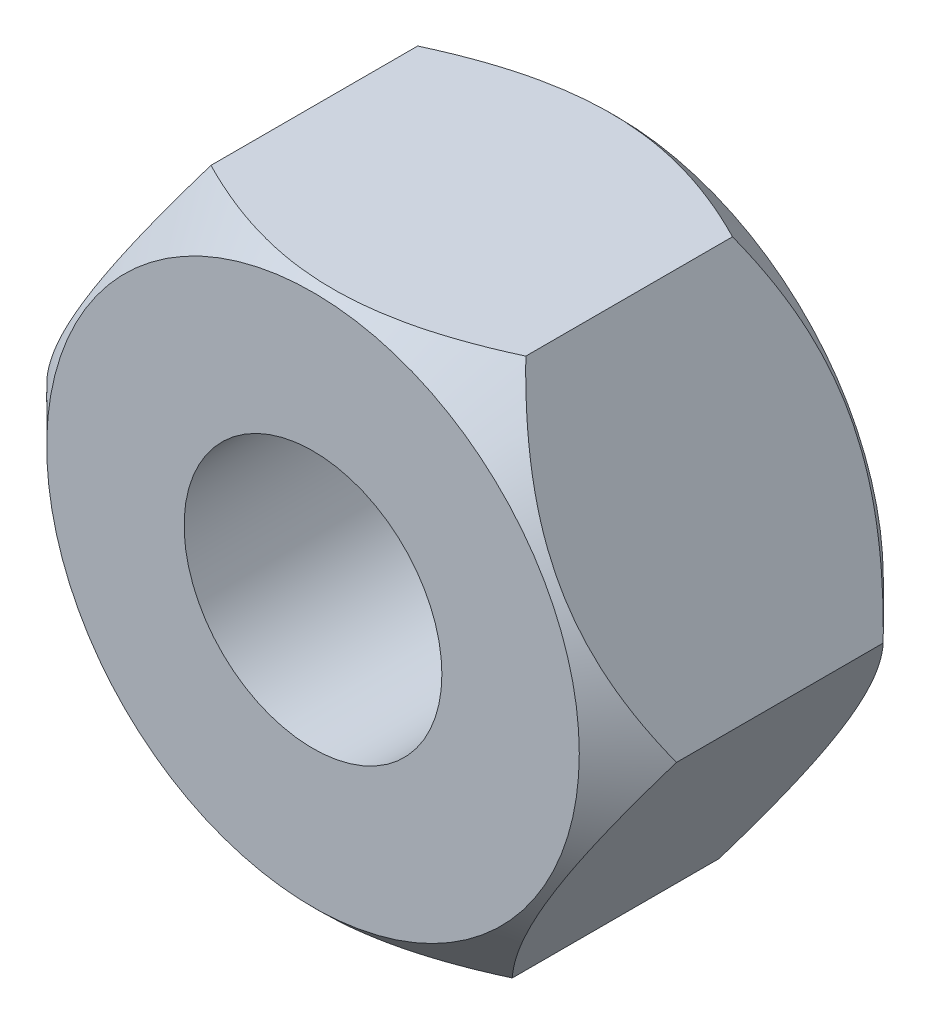
SolidWorks part; units mm, degrees
ref_plane "Front Plane" through (0, 0, 0) normal (0, 0, 1) x (1, 0, 0)
ref_plane "Top Plane" through (0, 0, 0) normal (0, 1, 0) x (1, 0, 0)
ref_plane "Right Plane" through (0, 0, 0) normal (1, 0, 0) x (0, 0, -1)
sketch "Sketch1" plane through (0, 0, 0) normal (0, 0, 1) x (1, 0, 0)
  circle A0 centre (0, 0) radius 1.59
  circle A1 centre (0, 0) radius 3.885
  dimension "D1" = 3.18
  dimension "D2" = 7.77
extrude "Boss-Extrude1" add sketch "Sketch1" along normal blind 3.75
chamfer "Chamfer1" distance 0.6 angle 45 2 edges at (3.885, 0, 0) (3.885, 0, 3.75)
sketch "Sketch2" plane through (0, 0, 0) normal (0, 0, -1) x (-1, 0, 0)
  line L1 (1.8588, 3.4115) -> (-2.025, 3.3155)
  line L2 (-2.025, 3.3155) -> (-3.8838, -0.096)
  line L3 (-3.8838, -0.096) -> (-1.8588, -3.4115)
  line L4 (-1.8588, -3.4115) -> (2.025, -3.3155)
  line L5 (2.025, -3.3155) -> (3.8838, 0.096)
  line L6 (3.8838, 0.096) -> (1.8588, 3.4115)
  circle A0 centre (0, 0) radius 3.3645 construction
  circle A1 centre (0, 0) radius 3.885 construction
  circle A2 centre (0, 0) radius 3.885
extrude "Cut-Extrude1" cut sketch "Sketch2" against normal blind 3.75 contours L2 A2 | L3 A2 | L4 A2 | L5 A2 | L6 A2 | L1 A2
thread "Thread1" pitch 0.3175 start angle 0, offset 0, length 0, pitch 0.3175, diameter 5.18
ref_plane "Plane2" through (-2.59, 0, 3.75) normal (0, -1, 0) x (-1, 0, 0)
sketch "Thread Profile2" plane through (-2.59, 0, 3.75) normal (0, -1, 0) x (-1, 0, 0)
  line L0 (0, 0) -> (0, 0.3175) construction
  line L1 (0, 0.2381) -> (-0.1719, 0.1389)
  line L2 (-0.1719, 0.1389) -> (-0.1719, 0.0992)
  line L3 (-0.1719, 0.0992) -> (0, 0)
  line L4 (-0.1719, 0.1191) -> (0, 0.1191) construction
  line L11 (0, 0.2381) -> (0, 0)
  point P6 (0, 0)
  dimension "Pitch" = 0.3175
  dimension "Profile_Angle" = 60
  dimension "Profile_Land" = 0.0397
  dimension "Profile_Height" = 0.1719
